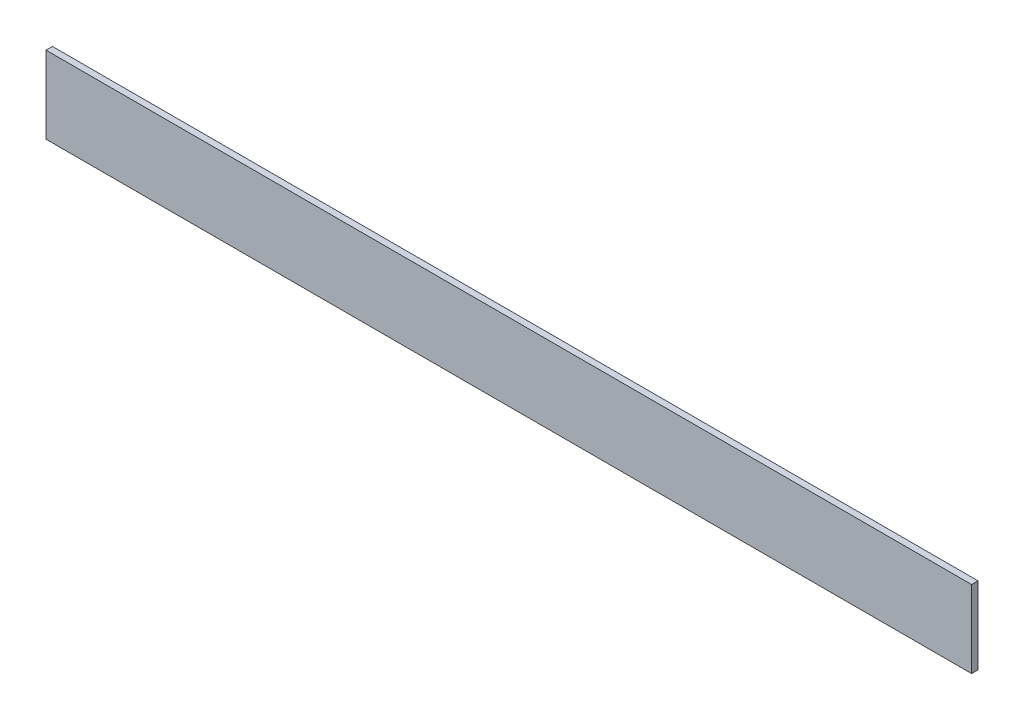
SolidWorks part; units mm, degrees
material "PVC 0.007 Plasticized"
ref_plane "Front Plane" through (0, 0, 0) normal (0, 0, 1) x (1, 0, 0)
ref_plane "Top Plane" through (0, 0, 0) normal (0, 1, 0) x (1, 0, 0)
ref_plane "Right Plane" through (0, 0, 0) normal (1, 0, 0) x (0, 0, -1)
sketch "Sketch1" plane through (0, 0, 0) normal (1, 0, 0) x (0, 0, -1)
  line L1 (-3.175, -38.1) -> (3.175, -38.1)
  line L2 (-3.175, -38.1) -> (-3.175, 38.1)
  line L3 (-3.175, 38.1) -> (3.175, 38.1)
  line L4 (3.175, -38.1) -> (3.175, 38.1)
  line L5 (-3.175, -38.1) -> (3.175, 38.1) construction
  line L6 (-3.175, 38.1) -> (3.175, -38.1) construction
  point P0 (0, 0)
  dimension "D1" = 76.2
  dimension "D2" = 6.35
extrude "Boss-Extrude1" add sketch "Sketch1" along normal blind 914.4
equation "\"D2@Sketch1\"=1in/4"
